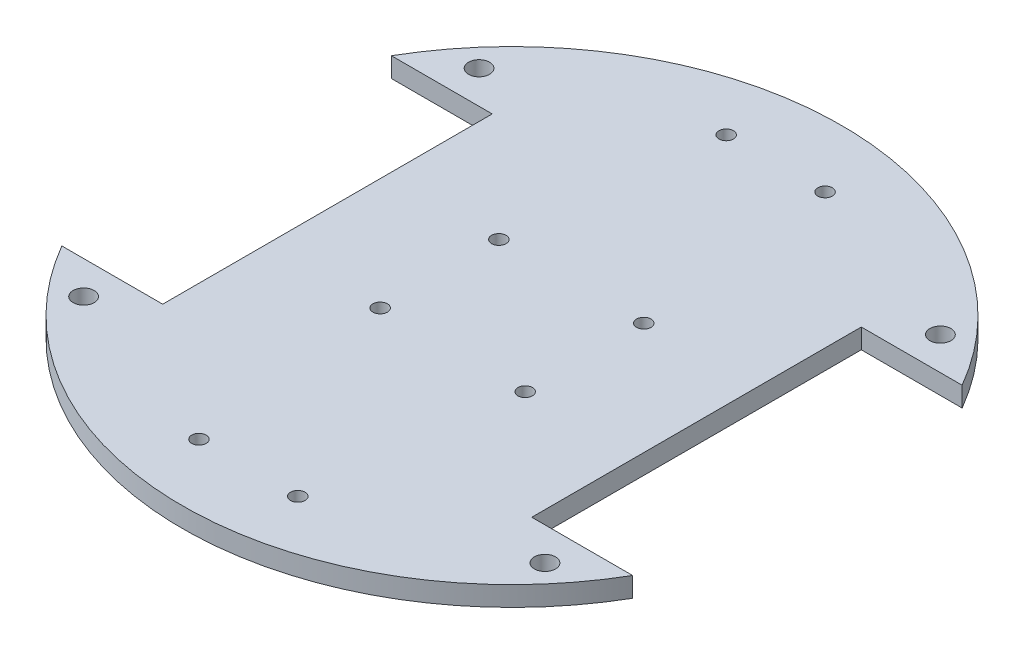
SolidWorks part; units mm, degrees
ref_plane "Front Plane" through (0, 0, 0) normal (0, 0, 1) x (1, 0, 0)
ref_plane "Top Plane" through (0, 0, 0) normal (0, 1, 0) x (1, 0, 0)
ref_plane "Right Plane" through (0, 0, 0) normal (1, 0, 0) x (0, 0, -1)
sketch "Sketch1" plane through (0, 0, 0) normal (0, 1, 0) x (1, 0, 0)
  line L0 (0, 50) -> (0, -50) construction
  line L1 (-50, 0) -> (50, 0) construction
  line L4 (-28, 25) -> (-28, -25)
  line L5 (-50, -25) -> (50, -25) construction
  line L6 (-50, -25) -> (-50, 25) construction
  line L7 (-50, 25) -> (50, 25) construction
  line L8 (50, -25) -> (50, 25) construction
  line L9 (-50, -25) -> (50, 25) construction
  line L10 (-50, 25) -> (50, -25) construction
  line L11 (-28, 25) -> (-43.3013, 25)
  line L12 (-28, -25) -> (-43.3013, -25)
  line L13 (28, 25) -> (28, -25)
  line L14 (28, 25) -> (43.3013, 25)
  line L15 (43.3013, -25) -> (28, -25)
  line L17 (-35, -30) -> (35, -30) construction
  line L18 (-35, -30) -> (-35, 30) construction
  line L19 (-35, 30) -> (35, 30) construction
  line L20 (35, -30) -> (35, 30) construction
  line L21 (-35, -30) -> (35, 30) construction
  line L22 (-35, 30) -> (35, -30) construction
  circle A1 centre (-11, 9) radius 1.1
  circle A6 centre (-7.5, 40) radius 1.1
  arc A10 (-43.3013, -25) -> (43.3013, -25) centre (0, 0) ccw
  circle A11 centre (-7.5, -40) radius 1.1
  circle A12 centre (-11, -9) radius 1.1
  circle A13 centre (7.5, -40) radius 1.1
  circle A14 centre (7.5, 40) radius 1.1
  circle A15 centre (11, 9) radius 1.1
  circle A16 centre (11, -9) radius 1.1
  arc A17 (43.3013, 25) -> (-43.3013, 25) centre (0, 0) ccw
  circle A18 centre (-35, 30) radius 1.6
  circle A19 centre (-35, -30) radius 1.6
  circle A20 centre (35, 30) radius 1.6
  circle A21 centre (35, -30) radius 1.6
  dimension "D1" = 100
  dimension "D2" = 2.2
  dimension "D7" = 2.2
  dimension "D13" = 3.2
  dimension "D3" = 11
  dimension "D4" = 9
  dimension "D5" = 40
  dimension "D6" = 7.5
  dimension "D8" = 100
  dimension "D9" = 50
  dimension "D10" = 17
  dimension "D11" = 70
  dimension "D12" = 60
extrude "Boss-Extrude1" add sketch "Sketch1" along normal blind 3
